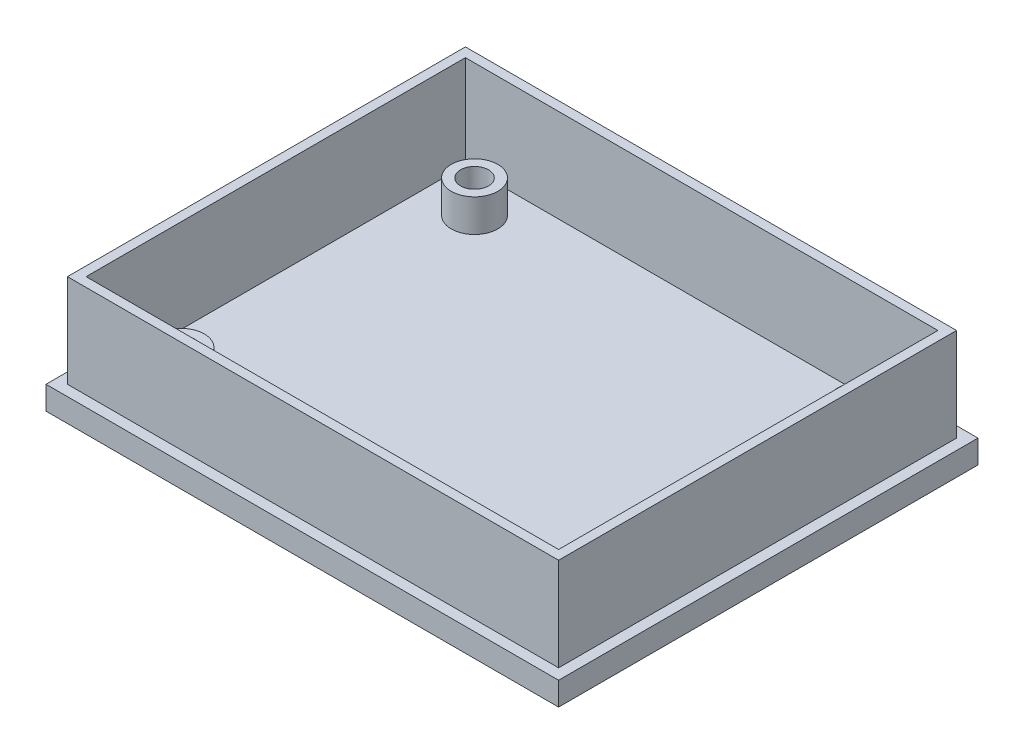
SolidWorks part; units mm, degrees
ref_plane "Front Plane" through (0, 0, 0) normal (0, 0, 1) x (1, 0, 0)
ref_plane "Top Plane" through (0, 0, 0) normal (0, 1, 0) x (1, 0, 0)
ref_plane "Right Plane" through (0, 0, 0) normal (1, 0, 0) x (0, 0, -1)
sketch "Sketch1" plane through (0, 0, 0) normal (0, 1, 0) x (1, 0, 0)
  line L1 (55, 45) -> (-55, 45)
  line L2 (55, 45) -> (55, -45)
  line L3 (55, -45) -> (-55, -45)
  line L4 (-55, 45) -> (-55, -45)
  line L5 (55, 45) -> (-55, -45) construction
  line L6 (55, -45) -> (-55, 45) construction
  point P0 (0, 0)
  dimension "D1" = 90
  dimension "D2" = 110
extrude "Boss-Extrude1" add sketch "Sketch1" along normal blind 5 contours L4 L3 L2 L1
sketch "Sketch4" plane through (0, 5, 0) normal (0, 1, 0) x (1, 0, 0)
  line L4 (-50.7, 40.7) -> (-50.7, -40.7)
  line L5 (-50.7, -40.7) -> (50.7, -40.7)
  line L6 (50.7, -40.7) -> (50.7, 40.7)
  line L7 (50.7, 40.7) -> (-50.7, 40.7)
  line L8 (52.7, 42.7) -> (-52.7, 42.7)
  line L9 (-52.7, 42.7) -> (-52.7, -42.7)
  line L10 (-52.7, -42.7) -> (52.7, -42.7)
  line L11 (52.7, -42.7) -> (52.7, 42.7)
  line L12 (52.7, 42.7) -> (-52.7, 42.7)
  line L13 (-52.7, 42.7) -> (-52.7, -42.7)
  line L14 (-52.7, -42.7) -> (52.7, -42.7)
  line L15 (52.7, -42.7) -> (52.7, 42.7)
  dimension "D1" = 2.3
  dimension "D2" = 2
extrude "Boss-Extrude2" add sketch "Sketch4" along normal blind 20
sketch "Sketch5" plane through (0, 5, 0) normal (0, 1, 0) x (1, 0, 0)
  circle A0 centre (-40.3803, 32.3418) radius 5
  circle A1 centre (-40.3803, -30.6582) radius 5
  circle A2 centre (42.6197, -30.6582) radius 5
  circle A3 centre (42.6197, 32.3418) radius 5
  point P8 (0, 0)
  dimension "D3" = 83
extrude "Boss-Extrude3" add sketch "Sketch5" along normal blind 7
sketch "Sketch6" plane through (0, 12, 0) normal (0, 1, 0) x (1, 0, 0)
  circle A18 centre (-40.3803, 32.3418) radius 3
  circle A19 centre (-40.3803, 32.3418) radius 3
  circle A21 centre (-40.3803, -30.6582) radius 3
  circle A22 centre (-40.3803, -30.6582) radius 3
  arc A24 (45.6197, -30.6582) -> (45.6197, -30.6582) centre (42.6197, -30.6582) ccw
  circle A25 centre (42.6197, -30.6582) radius 3
  arc A27 (45.6197, 32.3418) -> (45.6197, 32.3418) centre (42.6197, 32.3418) ccw
  circle A28 centre (42.6197, 32.3418) radius 3
  dimension "D1" = 2
  dimension "D2" = 2
  dimension "D3" = 2
  dimension "D4" = 2
extrude "Cut-Extrude1" cut sketch "Sketch6" against normal blind 5
